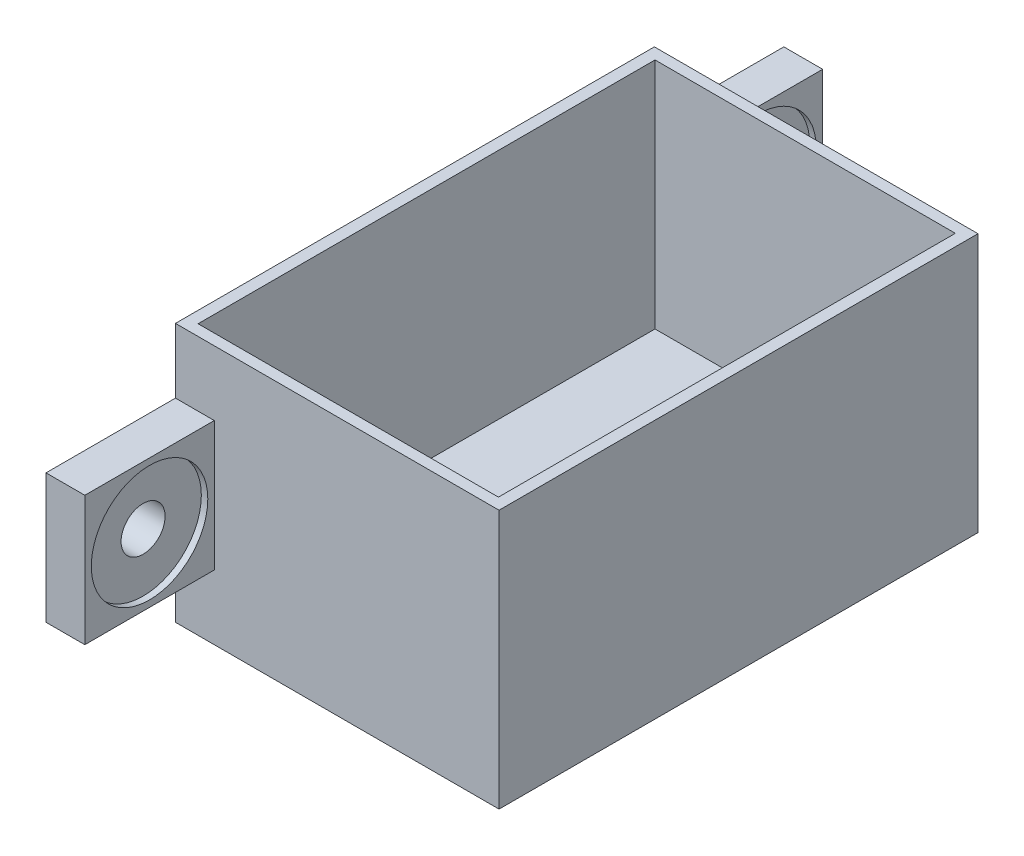
SolidWorks part; units mm, degrees
ref_plane "Front Plane" through (0, 0, 0) normal (0, 0, 1) x (1, 0, 0)
ref_plane "Top Plane" through (0, 0, 0) normal (0, 1, 0) x (1, 0, 0)
ref_plane "Right Plane" through (0, 0, 0) normal (1, 0, 0) x (0, 0, -1)
sketch "Sketch1" plane through (0, 0, 0) normal (0, 1, 0) x (1, 0, 0)
  line L1 (-88.7262, -7.5552) -> (-63.7262, -7.5552)
  line L2 (-88.7262, -7.5552) -> (-88.7262, 29.4448)
  line L3 (-88.7262, 29.4448) -> (-63.7262, 29.4448)
  line L4 (-63.7262, -7.5552) -> (-63.7262, 29.4448)
extrude "Boss-Extrude2" add sketch "Sketch1" along normal blind 20 contours L2 L1 L4 L3
sketch "Sketch4" plane through (0, 20, 0) normal (0, 1, 0) x (1, 0, 0)
  line L0 (-88.7262, 29.4448) -> (-63.7262, 29.4448) construction
  line L1 (-87.8262, 28.5948) -> (-64.6262, 28.5948)
  line L2 (-87.8262, 28.5948) -> (-87.8262, -6.7052)
  line L3 (-87.8262, -6.7052) -> (-64.6262, -6.7052)
  line L4 (-64.6262, 28.5948) -> (-64.6262, -6.7052)
  line L5 (-88.7262, -7.5552) -> (-63.7262, -7.5552) construction
  line L6 (-63.7262, -7.5552) -> (-63.7262, 29.4448) construction
  line L7 (-88.7262, -7.5552) -> (-88.7262, 29.4448) construction
  dimension "D1" = 0.85
  dimension "D2" = 0.85
  dimension "D3" = 0.9
  dimension "D4" = 0.9
extrude "Cut-Extrude1" cut sketch "Sketch4" against normal blind 18
ref_plane "Plane1" through (-88.7262, 0, -29.4448) normal (1, 0, 0) x (0, 0, -1)
sketch "Sketch30" plane through (-88.7262, 0, 0) normal (-1, 0, 0) x (0, 0, 1)
  line L0 (-29.4448, 20) -> (-29.4448, 0) construction
  line L1 (-29.4448, 15) -> (-39.4448, 15)
  line L2 (-29.4448, 15) -> (-29.4448, 5)
  line L3 (-29.4448, 5) -> (-39.4448, 5)
  line L4 (-39.4448, 15) -> (-39.4448, 5)
  line L6 (7.5552, 20) -> (7.5552, 0) construction
  line L7 (7.5552, 15) -> (17.5552, 15)
  line L8 (7.5552, 15) -> (7.5552, 5)
  line L9 (7.5552, 5) -> (17.5552, 5)
  line L10 (17.5552, 15) -> (17.5552, 5)
  dimension "D1" = 5
extrude "Boss-Extrude5" add sketch "Sketch30" against normal blind 3
hole_wizard "CBORE for M3 Hexagon head bolts-Full thread-grades AB5" positions "3DSketch4" profile "Sketch31" counterbore size "M3" standard "GB" end condition through all
sketch3d "3DSketch4"
  line L0 (-85.7262, 15, -29.4448) -> (-85.7262, 15, -39.4448) construction
  line L1 (-85.7262, 15, -39.4448) -> (-85.7262, 5, -39.4448) construction
  line L2 (-85.7262, 15, 17.5552) -> (-85.7262, 15, 7.5552) construction
  line L3 (-85.7262, 5, 17.5552) -> (-85.7262, 15, 17.5552) construction
  point P0 (-85.7262, 10, -34.4448)
  point P2 (-85.7262, 10, 12.5552)
  dimension "D1" = 5
  dimension "D2" = 5
  dimension "D3" = 5
  dimension "D4" = 5
sketch "Sketch31" plane through (-85.7262, 10, -34.4448) normal (0, 1, 0) x (0, 0, -1)
  line L0 (0, 0) -> (0, 3)
  line L1 (0, 3) -> (1.7, 3)
  line L3 (1.7, 3) -> (1.7, 0.5)
  line L4 (1.7, 0.5) -> (4.5, 0.5)
  line L5 (4.5, 0.5) -> (4.5, 0)
  line L7 (4.5, 0) -> (0, 0)
  line L11 (0, -6.35) -> (0, 107.95) construction
  dimension "Thru Hole Dia." = 3.4
  dimension "Thru Hole Depth" = 3
  dimension "C'Bore Dia." = 9
  dimension "C'Bore Depth" = 0.5
